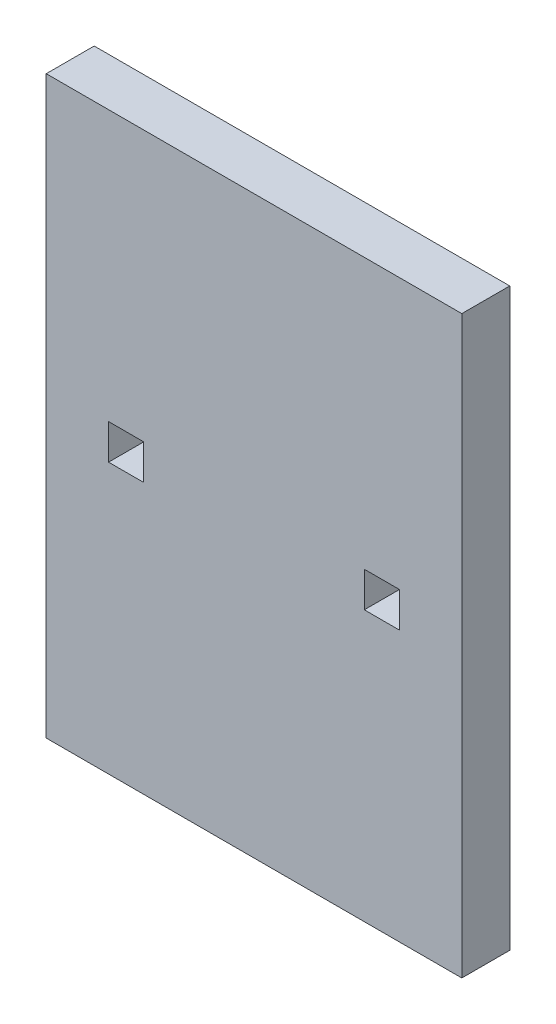
SolidWorks part; units mm, degrees
ref_plane "Front" through (0, 0, 0) normal (0, 0, 1) x (1, 0, 0)
ref_plane "Top" through (0, 0, 0) normal (0, 1, 0) x (1, 0, 0)
ref_plane "Right" through (0, 0, 0) normal (1, 0, 0) x (0, 0, -1)
sketch "Çizim1" plane through (0, 0, 0) normal (0, 0, 1) x (1, 0, 0)
  line L1 (0, 0) -> (260, 0)
  line L2 (0, 0) -> (0, -360)
  line L3 (0, -360) -> (260, -360)
  line L4 (260, 0) -> (260, -360)
  line L5 (39, -169) -> (61, -169)
  line L6 (39, -169) -> (39, -191)
  line L7 (39, -191) -> (61, -191)
  line L8 (61, -169) -> (61, -191)
  line L9 (39, -169) -> (61, -191) construction
  line L10 (39, -191) -> (61, -169) construction
  line L11 (199, -169) -> (221, -169)
  line L12 (199, -169) -> (199, -191)
  line L13 (199, -191) -> (221, -191)
  line L14 (221, -169) -> (221, -191)
  line L15 (199, -169) -> (221, -191) construction
  line L16 (199, -191) -> (221, -169) construction
  point P4 (50, -180)
  point P10 (210, -180)
  dimension "D1" = 260
  dimension "D2" = 360
  dimension "D3" = 22
  dimension "D4" = 22
  dimension "D5" = 22
  dimension "D6" = 22
  dimension "D7" = 180
  dimension "D8" = 50
  dimension "D9" = 210
extrude "Yükseklik-Ekstrüzyon1" add sketch "Çizim1" along normal blind 30
